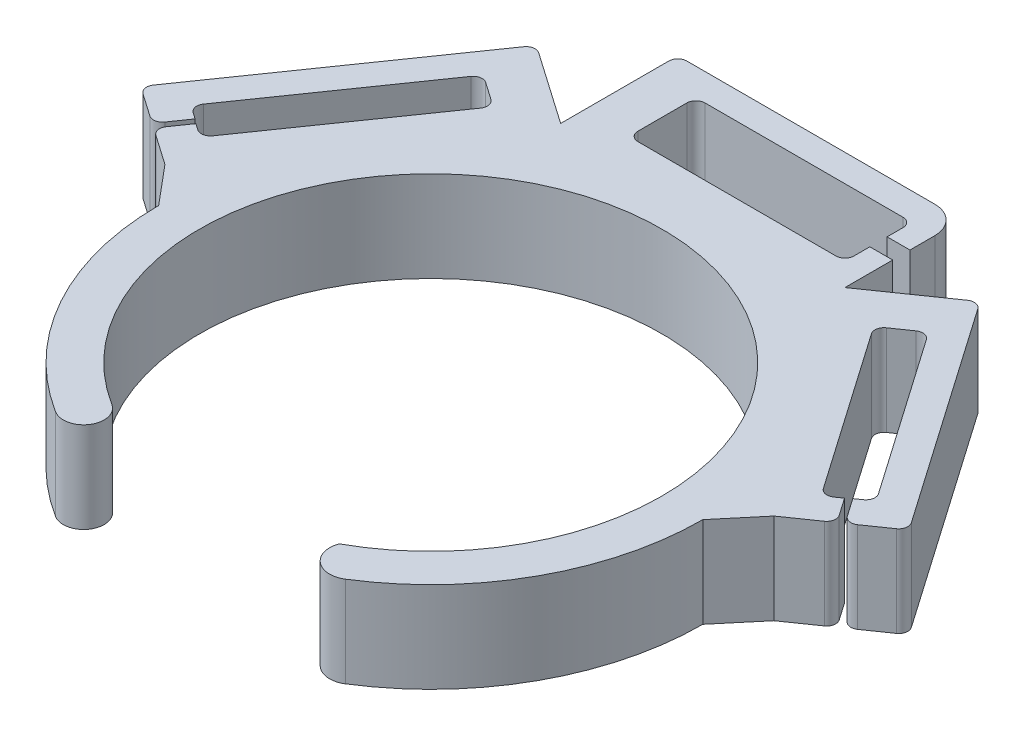
SolidWorks part; units mm, degrees
ref_plane "Front Plane" through (0, 0, 0) normal (0, 0, 1) x (1, 0, 0)
ref_plane "Top Plane" through (0, 0, 0) normal (0, 1, 0) x (1, 0, 0)
ref_plane "Right Plane" through (0, 0, 0) normal (1, 0, 0) x (0, 0, -1)
sketch "Sketch1" plane through (0, 0, 0) normal (0, 1, 0) x (1, 0, 0)
  line L0 (0, 0) -> (0, -25.5) construction
  line L1 (-15.9767, -25.3918) -> (0, 0) construction
  line L2 (0, 0) -> (15.9767, -25.3918) construction
  line L3 (-15.9767, -25.3918) -> (-13.5802, -21.5831) construction
  line L4 (-13.5802, -21.5831) -> (-15.9767, -25.3918) construction
  line L6 (-33.5777, 4.2677) -> (-15.674, 30)
  line L7 (33.5777, 4.2677) -> (15.674, 30)
  line L8 (0, 30) -> (-15.674, 30)
  line L9 (0, 30) -> (15.674, 30)
  line L10 (-33.5777, 4.2677) -> (-30, 0)
  line L11 (33.5777, 4.2677) -> (30, 0)
  line L12 (-15.674, 30) -> (-15.674, 41.9189)
  line L13 (-14.674, 42.9189) -> (12.674, 42.9189)
  line L14 (15.674, 39.9189) -> (15.674, 37.1732)
  line L15 (15.674, 30) -> (15.674, 35.2671)
  line L16 (15.674, 35.2671) -> (13.1556, 35.2671)
  line L17 (13.1556, 35.2671) -> (13.1556, 33.5214)
  line L18 (12.1556, 32.5214) -> (-9.674, 32.5214)
  line L19 (-10.674, 33.5214) -> (-10.674, 38.9189)
  line L20 (-9.674, 39.9189) -> (12.1556, 39.9189)
  line L21 (13.1556, 38.9189) -> (13.1556, 37.1732)
  line L22 (13.1556, 37.1732) -> (15.674, 37.1732)
  line L23 (-15.674, 30) -> (-23.6429, 35.5445)
  line L24 (-25.0349, 35.2948) -> (-41.7963, 11.2042)
  line L25 (-41.5466, 9.8122) -> (-39.027, 8.0591)
  line L26 (-37.635, 8.3089) -> (-36.2638, 10.2796)
  line L27 (-33.5777, 4.2677) -> (-36.8551, 6.548)
  line L28 (-37.1049, 7.94) -> (-35.7646, 9.8663)
  line L29 (-35.7646, 9.8663) -> (-35.0635, 9.3785)
  line L30 (-33.6715, 9.6282) -> (-21.5489, 27.0515)
  line L31 (-21.7987, 28.4435) -> (-23.731, 29.7879)
  line L32 (-25.123, 29.5382) -> (-37.2147, 12.1594)
  line L33 (-36.9649, 10.7674) -> (-36.2638, 10.2796)
  line L34 (41.5466, 9.8122) -> (39.027, 8.0591)
  line L35 (37.1049, 7.94) -> (35.7646, 9.8663)
  line L36 (35.7646, 9.8663) -> (35.0635, 9.3785)
  line L37 (36.9649, 10.7674) -> (36.2638, 10.2796)
  line L38 (37.635, 8.3089) -> (36.2638, 10.2796)
  line L39 (33.5777, 4.2677) -> (36.8551, 6.548)
  line L40 (21.7987, 28.4435) -> (23.731, 29.7879)
  line L41 (25.123, 29.5382) -> (37.2147, 12.1594)
  line L42 (33.6715, 9.6282) -> (21.5489, 27.0515)
  line L43 (25.0349, 35.2948) -> (41.7963, 11.2042)
  line L44 (15.674, 30) -> (23.6429, 35.5445)
  line L45 (33.5777, 4.2677) -> (15.674, 30)
  circle A0 centre (0, 0) radius 25.5
  arc A1 (-15.9767, -25.3918) -> (15.9767, -25.3918) centre (0, 0) cw
  arc A2 (-15.9767, -25.3918) -> (-13.5802, -21.5831) centre (-14.7784, -23.4874) ccw
  arc A3 (15.9767, -25.3918) -> (13.2866, -21.1165) centre (14.6317, -23.2541) cw
  arc A4 (12.674, 42.9189) -> (15.674, 39.9189) centre (12.674, 39.9189) cw
  arc A5 (12.1556, 39.9189) -> (13.1556, 38.9189) centre (12.1556, 38.9189) cw
  arc A6 (13.1556, 33.5214) -> (12.1556, 32.5214) centre (12.1556, 33.5214) cw
  arc A7 (-9.674, 32.5214) -> (-10.674, 33.5214) centre (-9.674, 33.5214) cw
  arc A8 (-14.674, 42.9189) -> (-15.674, 41.9189) centre (-14.674, 41.9189) ccw
  arc A9 (-10.674, 38.9189) -> (-9.674, 39.9189) centre (-9.674, 38.9189) cw
  arc A10 (-37.635, 8.3089) -> (-39.027, 8.0591) centre (-38.4558, 8.88) cw
  arc A11 (-37.1049, 7.94) -> (-36.8551, 6.548) centre (-36.284, 7.3689) ccw
  arc A12 (-41.5466, 9.8122) -> (-41.7963, 11.2042) centre (-40.9755, 10.6331) cw
  arc A13 (-23.6429, 35.5445) -> (-25.0349, 35.2948) centre (-24.214, 34.7237) ccw
  arc A14 (-25.123, 29.5382) -> (-23.731, 29.7879) centre (-24.3022, 28.9671) cw
  arc A15 (-21.5489, 27.0515) -> (-21.7987, 28.4435) centre (-22.3698, 27.6226) ccw
  arc A16 (-33.6715, 9.6282) -> (-35.0635, 9.3785) centre (-34.4923, 10.1994) cw
  arc A17 (-36.9649, 10.7674) -> (-37.2147, 12.1594) centre (-36.3938, 11.5883) cw
  arc A18 (41.5466, 9.8122) -> (41.7963, 11.2042) centre (40.9755, 10.6331) ccw
  arc A19 (37.635, 8.3089) -> (39.027, 8.0591) centre (38.4558, 8.88) ccw
  arc A20 (36.9649, 10.7674) -> (37.2147, 12.1594) centre (36.3938, 11.5883) ccw
  arc A21 (33.6715, 9.6282) -> (35.0635, 9.3785) centre (34.4923, 10.1994) ccw
  arc A22 (25.123, 29.5382) -> (23.731, 29.7879) centre (24.3022, 28.9671) ccw
  arc A23 (21.5489, 27.0515) -> (21.7987, 28.4435) centre (22.3698, 27.6226) cw
  arc A24 (23.6429, 35.5445) -> (25.0349, 35.2948) centre (24.214, 34.7237) cw
  arc A25 (37.1049, 7.94) -> (36.8551, 6.548) centre (36.284, 7.3689) cw
  point P12 (14.6351, -23.4874)
  point P13 (0, 30)
  point P16 (-24.6258, 17.1338)
  point P19 (24.6258, 17.1338)
  point P20 (0, 0)
  dimension "D1" = 51
  dimension "D4" = 30
  dimension "D7" = 3
  dimension "D8" = 1
  dimension "D9" = 1
  dimension "D10" = 1
  dimension "D5" = 5
  dimension "D6" = 3
extrude "Boss-Extrude1" add sketch "Sketch1" along normal blind 10 contours A3 A1 A2 A0 | L10 A1 L6 | L33 A17 L32 A14 L31 A15 L30 A16 L29 L28 A11 L27 L6 L23 A13 L24 A12 L25 A10 L26 | L19 A9 L20 A5 L21 L22 L14 A4 L13 A8 L12 L8 L9 L15 L16 L17 A6 L18 A7 | A25 L35 L36 A21 L42 A23 L40 A22 L41 A20 L37 L38 A19 L34 A18 L43 A24 L44 L45 L7 L39 | L6 A1 L8 | L9 A1 L45 | L7 A1 L11
